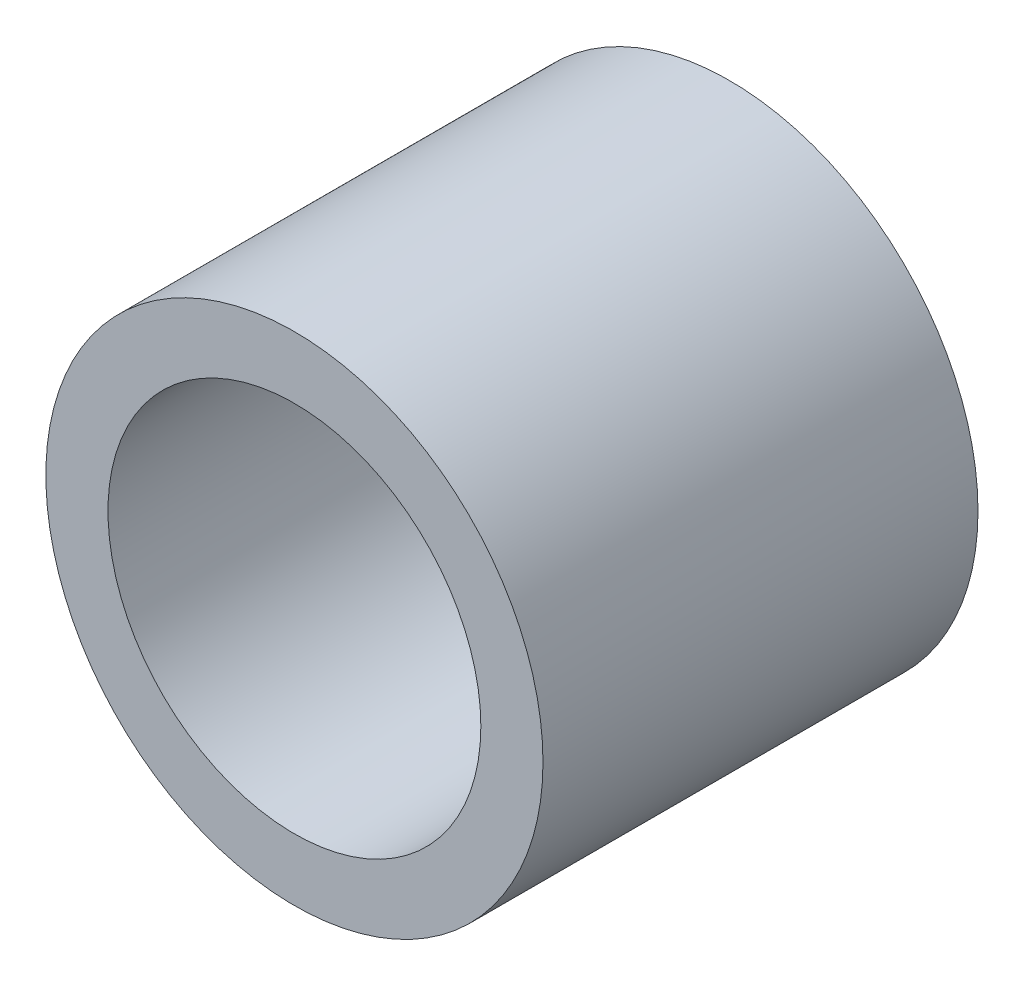
SolidWorks part; units mm, degrees
ref_plane "Front Plane" through (0, 0, 0) normal (0, 0, 1) x (1, 0, 0)
ref_plane "Top Plane" through (0, 0, 0) normal (0, 1, 0) x (1, 0, 0)
ref_plane "Right Plane" through (0, 0, 0) normal (1, 0, 0) x (0, 0, -1)
sketch "Sketch1" plane through (0, 0, 0) normal (0, 0, 1) x (1, 0, 0)
  circle A0 centre (0, 0) radius 2
  circle A1 centre (0, 0) radius 1.5
  dimension "D1" = 4
  dimension "D2" = 3
extrude "Boss-Extrude1" add sketch "Sketch1" along normal blind 3.5
